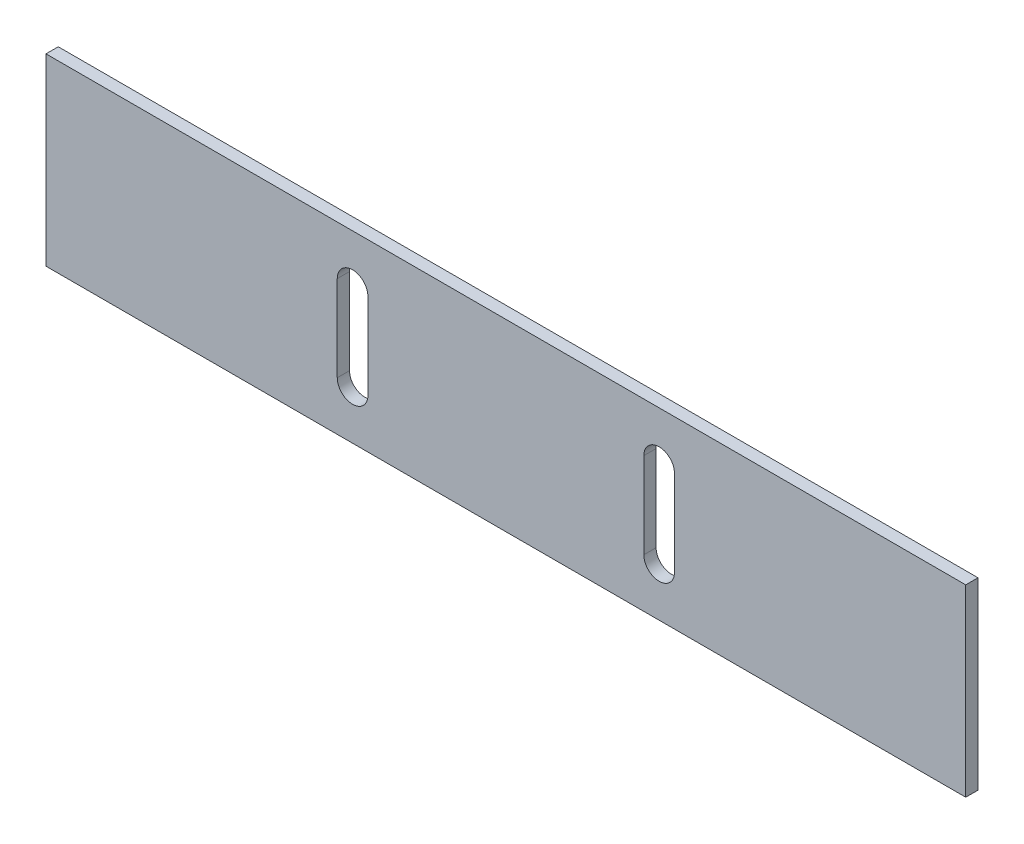
SolidWorks part; units mm, degrees
ref_plane "Спереди" through (0, 0, 0) normal (0, 0, 1) x (1, 0, 0)
ref_plane "Сверху" through (0, 0, 0) normal (0, 1, 0) x (1, 0, 0)
ref_plane "Справа" through (0, 0, 0) normal (1, 0, 0) x (0, 0, -1)
sketch "Эскиз1" plane through (0, 0, 0) normal (0, 0, 1) x (1, 0, 0)
  line L0 (31.1189, 15) -> (66.2351, 15) construction
  line L1 (0, 0) -> (150, 0)
  line L2 (0, 0) -> (0, 30)
  line L3 (0, 30) -> (150, 30)
  line L4 (150, 0) -> (150, 30)
  line L5 (47.5, 8) -> (47.5, 22)
  line L6 (52.5, 22) -> (52.5, 8)
  line L7 (97.5, 8) -> (97.5, 22)
  line L8 (102.5, 22) -> (102.5, 8)
  arc A0 (47.5, 22) -> (52.5, 22) centre (50, 22) cw
  arc A1 (47.5, 8) -> (52.5, 8) centre (50, 8) ccw
  arc A2 (97.5, 22) -> (102.5, 22) centre (100, 22) cw
  arc A3 (97.5, 8) -> (102.5, 8) centre (100, 8) ccw
  dimension "D1" = 2
extrude "Бобышка-Вытянуть1" add sketch "Эскиз1" along normal blind 2
